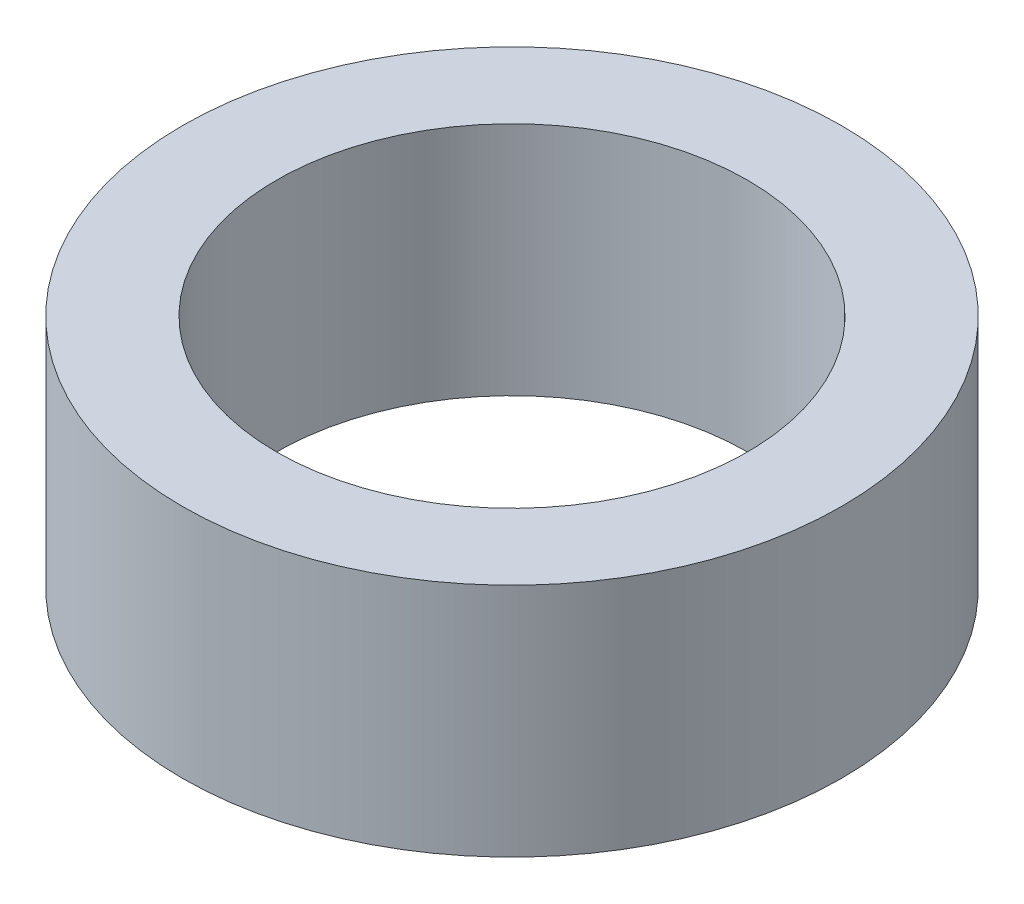
SolidWorks part; units mm, degrees
ref_plane "Front Plane" through (0, 0, 0) normal (0, 0, 1) x (1, 0, 0)
ref_plane "Top Plane" through (0, 0, 0) normal (0, 1, 0) x (1, 0, 0)
ref_plane "Right Plane" through (0, 0, 0) normal (1, 0, 0) x (0, 0, -1)
sketch "Sketch1" plane through (0, 0, 0) normal (0, 0, 1) x (1, 0, 0)
  line L0 (0, 0) -> (0, -1.5736) construction
  line L1 (-3.175, 0) -> (-4.445, 0)
  line L2 (-3.175, 0) -> (-3.175, -3.175)
  line L3 (-3.175, -3.175) -> (-4.445, -3.175)
  line L4 (-4.445, 0) -> (-4.445, -3.175)
  dimension "D1" = 3.175
  dimension "D2" = 4.445
  dimension "D3" = 3.175
revolve "Revolve1" add sketch "Sketch1" angle 360 about L0
